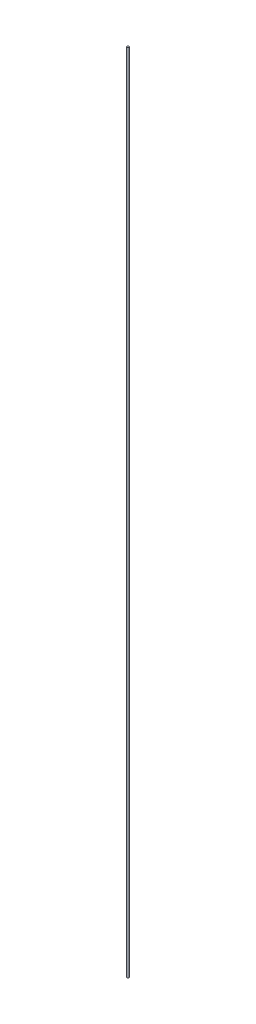
SolidWorks part; units mm, degrees
ref_plane "前视基准面" through (0, 0, 0) normal (0, 0, 1) x (1, 0, 0)
ref_plane "上视基准面" through (0, 0, 0) normal (0, 1, 0) x (1, 0, 0)
ref_plane "右视基准面" through (0, 0, 0) normal (1, 0, 0) x (0, 0, -1)
sketch "草图1" plane through (0, 0, 0) normal (0, 1, 0) x (1, 0, 0)
  circle A0 centre (0, 0) radius 1
extrude "凸台-拉伸1" add sketch "草图1" along normal blind 800
sketch "草图2" plane through (0, 800, 0) normal (0, 1, 0) x (1, 0, 0)
  line L0 (-2, 0) -> (2, 0)
  line L1 (0, 2) -> (0, -2)
  circle A0 centre (0, 0) radius 2
sketch "草图3" plane through (0, 0, 0) normal (0, -1, 0) x (1, 0, 0)
  line L0 (-2, 0) -> (2, 0)
  line L1 (0, 2) -> (0, -2)
  circle A0 centre (0, 0) radius 2
